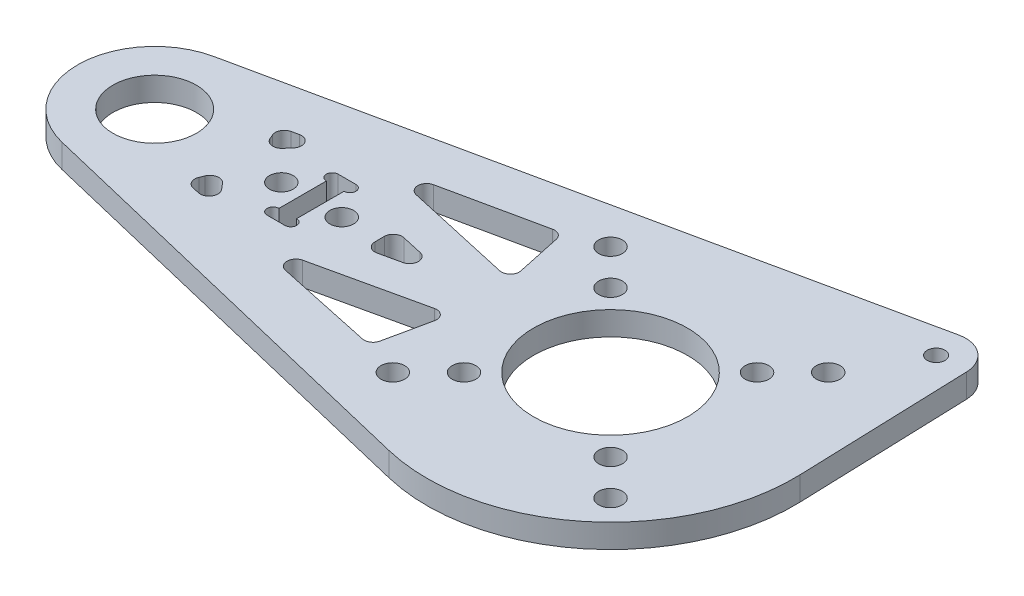
SolidWorks part; units mm, degrees
material "Thornel Mat VMA"
ref_plane "前视基准面" through (0, 0, 0) normal (0, 0, 1) x (1, 0, 0)
ref_plane "上视基准面" through (0, 0, 0) normal (0, 1, 0) x (1, 0, 0)
ref_plane "右视基准面" through (0, 0, 0) normal (1, 0, 0) x (0, 0, -1)
sketch "草图1" plane through (0, 0, 0) normal (0, 1, 0) x (1, 0, 0)
  line L0 (-79.7193, 12.7124) -> (23.9541, 34.8894)
  line L5 (-77, 0) -> (0, 0) construction
  line L6 (-80.039, -12.6398) -> (-7.2468, -30.1411)
  line L7 (0, 0) -> (25, 30) construction
  line L10 (-18.3848, 18.3848) -> (0, 0) construction
  line L11 (29.9971, 30.169) -> (30.9823, 1.0481)
  circle A0 centre (-77, 0) radius 7.05
  arc A1 (-79.7193, 12.7124) -> (-80.039, -12.6398) centre (-77, 0) ccw
  arc A7 (-7.2468, -30.1411) -> (30.9823, 1.0481) centre (0, 0) ccw
  circle A8 centre (25, 30) radius 1.5
  circle A9 centre (0, 0) radius 26 construction
  circle A10 centre (-18.3848, 18.3848) radius 2
  circle A11 centre (18.3848, 18.3848) radius 2
  circle A12 centre (18.3848, -18.3848) radius 2
  circle A13 centre (-18.3848, -18.3848) radius 2
  arc A14 (29.9971, 30.169) -> (23.9541, 34.8894) centre (25, 30) ccw
  circle A17 centre (0, 0) radius 17.5 construction
  circle A18 centre (-12.3744, 12.3744) radius 2
  circle A19 centre (12.3744, 12.3744) radius 2
  circle A20 centre (12.3744, -12.3744) radius 2
  circle A21 centre (-12.3744, -12.3744) radius 2
  circle A22 centre (0, 0) radius 13
  circle A23 centre (0, 0) radius 28 construction
  dimension "D3" = 14.1
  dimension "D4" = 25
  dimension "D7" = 3
  dimension "D5" = 30
  dimension "D6" = 26
  dimension "D2" = 52
  dimension "D10" = 5
  dimension "D12" = 5
  dimension "D13" = 4
  dimension "D14" = 4
  dimension "D15" = 35
  dimension "D16" = 2
  dimension "D18" = 26
  dimension "D1" = 77
  dimension "D8" = 4
  dimension "D9" = 45
extrude "凸台-拉伸1" add sketch "草图1" along normal blind 4
sketch "草图4" plane through (0, 4, 0) normal (0, 1, 0) x (1, 0, 0)
  line L0 (-52, 0) -> (0, 0) construction
  line L1 (-52, -6) -> (-49, -6)
  line L2 (-52, -6) -> (-52, 6)
  line L3 (-52, 6) -> (-49, 6)
  line L4 (-49, -6) -> (-49, 6)
  circle A1 centre (-77, 0) radius 7.05 construction
  circle A2 centre (-55.6, 0) radius 2
  circle A3 centre (-45.4, 0) radius 2
  dimension "D2" = 25
  dimension "D4" = 3.6
  dimension "D5" = 4
  dimension "D6" = 3.6
  dimension "D1" = 3
  dimension "D3" = 12
extrude "切除-拉伸7" cut sketch "草图4" against normal through all
sketch "草图8" plane through (0, 4, 0) normal (0, 1, 0) x (1, 0, 0)
  line L21 (-52, 6) -> (-52, -6) construction
  line L22 (-49, -6) -> (-49, 6) construction
  circle A17 centre (-52, 5) radius 1
  circle A18 centre (-52, -5) radius 1
  circle A19 centre (-49, -5) radius 1
  circle A20 centre (-49, 5) radius 1
  dimension "D1" = 2
extrude "切除-拉伸6" cut sketch "草图8" against normal through all
sketch "草图9" plane through (0, 4, 0) normal (0, 1, 0) x (1, 0, 0)
  line L0 (-24.3699, 16.3713) -> (-21.9374, 5)
  line L1 (-21.9374, 5) -> (-49.1156, 11.0779)
  line L2 (-49.1156, 11.0779) -> (-24.3699, 16.3713)
  line L6 (-2.2, 0) -> (2.2, 0) construction
  line L7 (-49.1156, -11.0779) -> (-24.3699, -16.3713)
  line L8 (-21.9374, -5) -> (-49.1156, -11.0779)
  line L9 (-24.3699, -16.3713) -> (-21.9374, -5)
  line L10 (0, 0) -> (-18.3848, 18.3848) construction
  line L11 (23.9541, 34.8894) -> (-79.7193, 12.7124) construction
  line L19 (-64.1648, 7.8587) -> (-56.7031, 9.4549)
  line L20 (-56.7031, 9.4549) -> (-62.252, 3)
  line L21 (-56.7031, -9.4549) -> (-62.252, -3)
  line L22 (-64.1648, -7.8587) -> (-56.7031, -9.4549)
  line L23 (-39, 2.6676) -> (-27.0717, 0)
  line L24 (-39, 2.6676) -> (-39, -2.6676)
  line L25 (-49, -4) -> (-49, 4) construction
  line L26 (-39, -2.6676) -> (-27.0717, 0)
  circle A0 centre (0, 0) radius 22.5 construction
  arc A1 (-62.252, 3) -> (-64.1648, 7.8587) centre (-77, 0) ccw
  circle A2 centre (-77, 0) radius 7.05 construction
  arc A3 (-62.252, -3) -> (-64.1648, -7.8587) centre (-77, 0) cw
  circle A4 centre (-55.6, 0) radius 2 construction
  circle A5 centre (-45.4, 0) radius 2 construction
  dimension "D1" = 45
  dimension "D6" = 8
  dimension "D4" = 10
  dimension "D2" = 10
  dimension "D3" = 8
  dimension "D5" = 10
  dimension "D7" = 6
  dimension "D8" = 7
  dimension "D9" = 6
extrude "切除-拉伸8" cut sketch "草图9" against normal through all
fillet "圆角1" radius 1.5 15 edges at (-21.9374, 2, -5) (-49.1156, 2, -11.0779) (-24.3699, 2, -16.3713) (-56.7031, 2, 9.4549) (-62.252, 2, 3) (-24.3699, 2, 16.3713) (-49.1156, 2, 11.0779) (-21.9374, 2, 5) (-56.7031, 2, -9.4549) (-62.252, 2, -3) (-64.1648, 2, -7.8587) (-64.1648, 2, 7.8587) (-27.0717, 2, 0) (-39, 2, 2.6676) (-39, 2, -2.6676)
